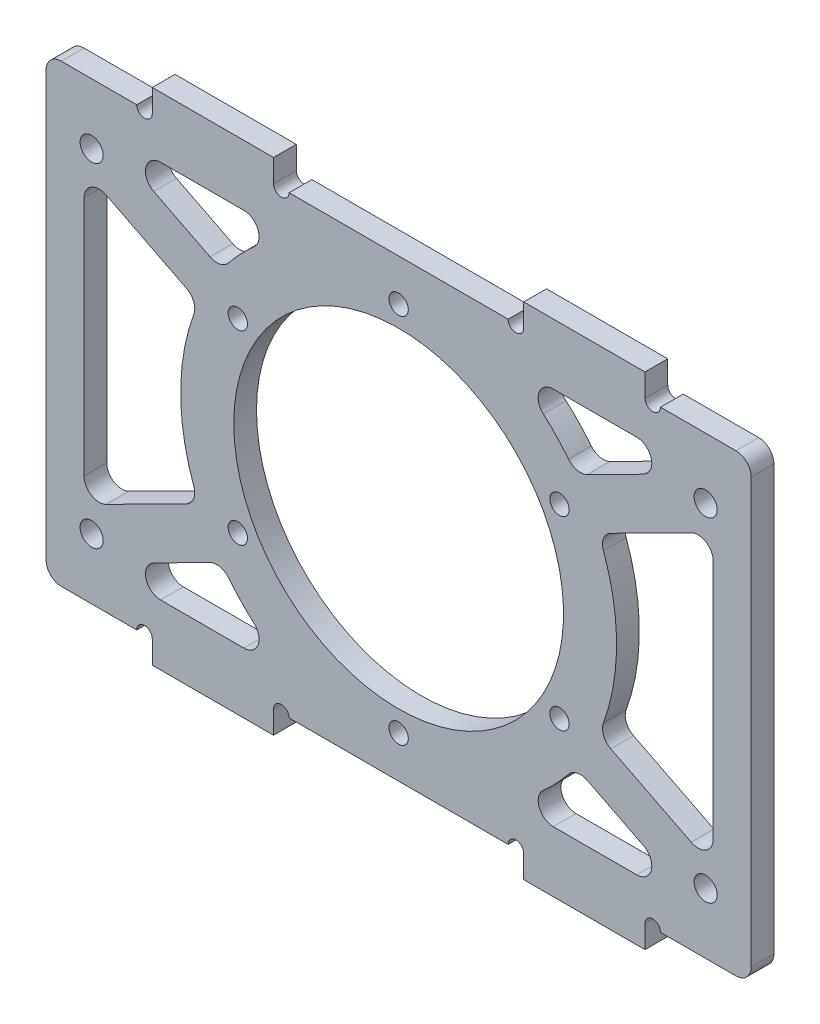
SolidWorks part; units mm, degrees
material "Thornel Mat VMA"
ref_plane "前视基准面" through (0, 0, 0) normal (0, 0, 1) x (1, 0, 0)
ref_plane "上视基准面" through (0, 0, 0) normal (0, 1, 0) x (1, 0, 0)
ref_plane "右视基准面" through (0, 0, 0) normal (1, 0, 0) x (0, 0, -1)
sketch "草图1" plane through (0, 0, 0) normal (0, 0, 1) x (1, 0, 0)
  line L1 (-46.5, -30) -> (46.5, -30)
  line L2 (-46.5, -30) -> (-46.5, 30)
  line L3 (-46.5, 30) -> (46.5, 30)
  line L4 (46.5, -30) -> (46.5, 30)
  line L5 (0, 30) -> (0, -30) construction
  line L6 (-46.5, 0) -> (46.5, 0) construction
  point P0 (0, 0)
  dimension "D1" = 60
  dimension "D2" = 93
extrude "凸台-拉伸1" add sketch "草图1" along normal mid plane 3
sketch "草图2" plane through (0, 0, 1.5) normal (0, 0, 1) x (1, 0, 0)
  circle A0 centre (0, 0) radius 21.75
  dimension "D1" = 43.5
extrude "切除-拉伸1" cut sketch "草图2" against normal mid plane 24
sketch "草图3" plane through (0, 0, 1.5) normal (0, 0, 1) x (1, 0, 0)
  line L0 (0, 24.5) -> (0, 0) construction
  line L1 (0, 0) -> (21.2176, 12.25) construction
  circle A0 centre (0, 0) radius 24.5 construction
  circle A1 centre (21.2176, 12.25) radius 1.275
  circle A2 centre (21.2176, -12.25) radius 1.275
  circle A3 centre (0, -24.5) radius 1.275
  circle A4 centre (-21.2176, -12.25) radius 1.275
  circle A5 centre (-21.2176, 12.25) radius 1.275
  circle A6 centre (0, 24.5) radius 1.275
  point P17 (0, 0)
  dimension "D1" = 49
  dimension "D2" = 2.55
  dimension "D4" = 60
  dimension "D3" = 6
extrude "切除-拉伸2" cut sketch "草图3" against normal mid plane 24
sketch "草图4" plane through (0, 0, 1.5) normal (0, 0, 1) x (1, 0, 0)
  line L0 (40.5, -22) -> (40.5, 22) construction
  line L1 (0, 0) -> (40.5, 0) construction
  line L2 (46.5, -30) -> (46.5, 30) construction
  line L3 (46.5, 30) -> (-46.5, 30) construction
  line L4 (0, 0) -> (0, 37.3634) construction
  circle A0 centre (40.5, -22) radius 1.525
  circle A1 centre (40.5, 22) radius 1.525
  circle A2 centre (-40.5, -22) radius 1.525
  circle A3 centre (-40.5, 22) radius 1.525
  point P3 (40.5, 0)
  dimension "D3" = 3.05
  dimension "D1" = 6
  dimension "D2" = 8
extrude "切除-拉伸3" cut sketch "草图4" against normal mid plane 30
sketch "草图5" [suppressed] plane through (0, 0, 1.5) normal (0, 0, 1) x (1, 0, 0)
  circle A0 centre (0, 0) radius 19 construction
  circle A1 centre (0, 19) radius 1.275
  circle A2 centre (13.435, 13.435) radius 1.275
  circle A3 centre (19, 0) radius 1.275
  circle A4 centre (13.435, -13.435) radius 1.275
  circle A5 centre (0, -19) radius 1.275
  circle A6 centre (-13.435, -13.435) radius 1.275
  circle A7 centre (-19, 0) radius 1.275
  circle A8 centre (-13.435, 13.435) radius 1.275
  point P21 (0, 0)
  dimension "D1" = 38
  dimension "D2" = 2.55
  dimension "D3" = 8
extrude "切除-拉伸4" [suppressed] cut sketch "草图5" against normal mid plane 30
sketch "草图6" plane through (0, 0, 1.5) normal (0, 0, 1) x (1, 0, 0)
  line L0 (21.2176, 12.25) -> (40.5, 22) construction
  line L1 (26.3558, 11.4864) -> (41.5, 19.1439)
  line L2 (41.5, 19.1439) -> (41.5, -19.1439)
  line L3 (41.5, -19.1439) -> (26.3558, -11.4864)
  line L4 (0, 0) -> (41.5, 0) construction
  line L5 (46.5, -30) -> (46.5, 30) construction
  arc A0 (26.3558, -11.4864) -> (26.3558, 11.4864) centre (0, 0) ccw
  circle A1 centre (0, 0) radius 21.75 construction
  dimension "D1" = 7
  dimension "D2" = 3
  dimension "D3" = 5
extrude "切除-拉伸5" cut sketch "草图6" against normal blind 10
mirror "镜向1" about plane through (0, 0, 0) normal (1, 0, 0) of "切除-拉伸5"
fillet "圆角1" radius 2 12 edges at (-41.5, -19.1439, 0) (-41.5, 19.1439, 0) (46.5, 30, 0) (-46.5, 30, 0) (-46.5, -30, 0) (46.5, -30, 0) (26.3558, 11.4864, 0) (41.5, 19.1439, 0) (41.5, -19.1439, 0) (26.3558, -11.4864, 0) (-26.3558, -11.4864, 0) (-26.3558, 11.4864, 0)
sketch "草图8" plane through (0, 0, 1.5) normal (0, 0, 1) x (1, 0, 0)
  line L0 (14.1973, 25) -> (39.7847, 25)
  line L1 (39.7847, 25) -> (23.3938, 16.7121)
  line L2 (38.5975, 17.6763) -> (27.9893, 12.3123) construction
  line L3 (44.5, 30) -> (-44.5, 30) construction
  line L4 (0, 0) -> (62.8695, 0) construction
  line L5 (39.7847, -25) -> (23.3938, -16.7121)
  line L6 (14.1973, -25) -> (39.7847, -25)
  arc A0 (23.3938, 16.7121) -> (14.1973, 25) centre (0, 0) ccw
  arc A1 (27.0126, -9.8428) -> (27.0126, 9.8428) centre (0, 0) ccw construction
  arc A2 (23.3938, -16.7121) -> (14.1973, -25) centre (0, 0) cw
  dimension "D1" = 6
  dimension "D2" = 5
extrude "切除-拉伸6" cut sketch "草图8" against normal blind 10
mirror "镜向2" about plane through (0, 0, 0) normal (1, 0, 0) of "切除-拉伸6"
fillet "圆角2" radius 2 12 edges at (-39.7847, 25, 0) (-39.7847, -25, 0) (-23.3938, -16.7121, 0) (-14.1973, -25, 0) (23.3938, -16.7121, 0) (39.7847, -25, 0) (14.1973, -25, 0) (14.1973, 25, 0) (39.7847, 25, 0) (23.3938, 16.7121, 0) (-14.1973, 25, 0) (-23.3938, 16.7121, 0)
sketch "草图9" [suppressed] plane through (0, 0, 1.5) normal (0, 0, 1) x (1, 0, 0)
  line L0 (40.5, 22) -> (19, 0) construction
  line L1 (19, 0) -> (40.5, -22) construction
  line L2 (40.5, 17.907) -> (23, 0)
  line L3 (23, 0) -> (40.5, -17.907)
  line L4 (40.5, 17.907) -> (40.5, -17.907)
  line L5 (46.5, -30) -> (46.5, 30) construction
  line L6 (0, 0) -> (0, -19) construction
  line L7 (-40.5, 17.907) -> (-23, 0) construction
  line L8 (-23, 0) -> (-40.5, -17.907) construction
  line L9 (-40.5, 17.907) -> (-40.5, -17.907) construction
  line L10 (0, 30) -> (0, 15) construction
  line L11 (46.5, 30) -> (-46.5, 30) construction
  line L12 (37.2826, 23) -> (21.8434, 7.2018)
  line L13 (37.2826, 23) -> (0, 23)
  line L14 (0, 0) -> (15, 0) construction
  line L15 (37.2826, -23) -> (0, -23)
  line L16 (37.2826, -23) -> (21.8434, -7.2018)
  circle A1 centre (0, 0) radius 15 construction
  arc A2 (21.8434, 7.2018) -> (0, 23) centre (0, 0) ccw
  arc A3 (21.8434, -7.2018) -> (0, -23) centre (0, 0) cw
  dimension "D1" = 23
  dimension "D2" = 6
  dimension "D3" = 3
  dimension "D4" = 2.8607
extrude "切除-拉伸7" [suppressed] cut sketch "草图9" against normal blind 10
fillet "圆角3" [suppressed] radius 2
mirror "镜向3" [suppressed] about plane through (0, 0, 0) normal (1, 0, 0)
fillet "圆角4" [suppressed] radius 2
sketch "草图10" plane through (0, 0, -1.5) normal (0, 0, -1) x (-1, 0, 0)
  line L0 (-44.5, 30) -> (44.5, 30) construction
  line L1 (-32.5, 27) -> (-16.5, 27)
  line L2 (-32.5, 27) -> (-32.5, 33)
  line L3 (-32.5, 33) -> (-16.5, 33)
  line L4 (-16.5, 27) -> (-16.5, 33)
  line L5 (-32.5, 27) -> (-16.5, 33) construction
  line L6 (-32.5, 33) -> (-16.5, 27) construction
  line L7 (-46.5, -28) -> (-46.5, 28) construction
  point P0 (-24.5, 30)
  dimension "D1" = 3
  dimension "D2" = 14
  dimension "D3" = 16
extrude "凸台-拉伸2" add sketch "草图10" against normal up to surface (3 mm away) up to face at (-25.1264, -21.4383, 1.5)
mirror "镜向4" about plane through (0, 0, 0) normal (1, 0, 0) of "凸台-拉伸2"
mirror "镜向5" about plane through (0, 0, 0) normal (0, 1, 0) of "镜向4", "凸台-拉伸2"
sketch "草图11" plane through (0, 0, 1.5) normal (0, 0, 1) x (1, 0, 0)
  line L0 (44.5, 30) -> (32.5, 30) construction
  line L1 (16.5, 30) -> (-16.5, 30) construction
  line L2 (-32.5, 30) -> (-44.5, 30) construction
  line L3 (-44.5, -30) -> (-32.5, -30) construction
  line L4 (-16.5, -30) -> (16.5, -30) construction
  line L5 (32.5, -30) -> (44.5, -30) construction
  circle A0 centre (33.525, 30) radius 1.025
  circle A1 centre (15.475, 30) radius 1.025
  circle A2 centre (-15.475, 30) radius 1.025
  circle A3 centre (-33.525, 30) radius 1.025
  circle A4 centre (-33.525, -30) radius 1.025
  circle A5 centre (-15.475, -30) radius 1.025
  circle A6 centre (15.475, -30) radius 1.025
  circle A7 centre (33.525, -30) radius 1.025
  dimension "D1" = 2.05
extrude "切除-拉伸8" cut sketch "草图11" against normal up to surface (3 mm away)
